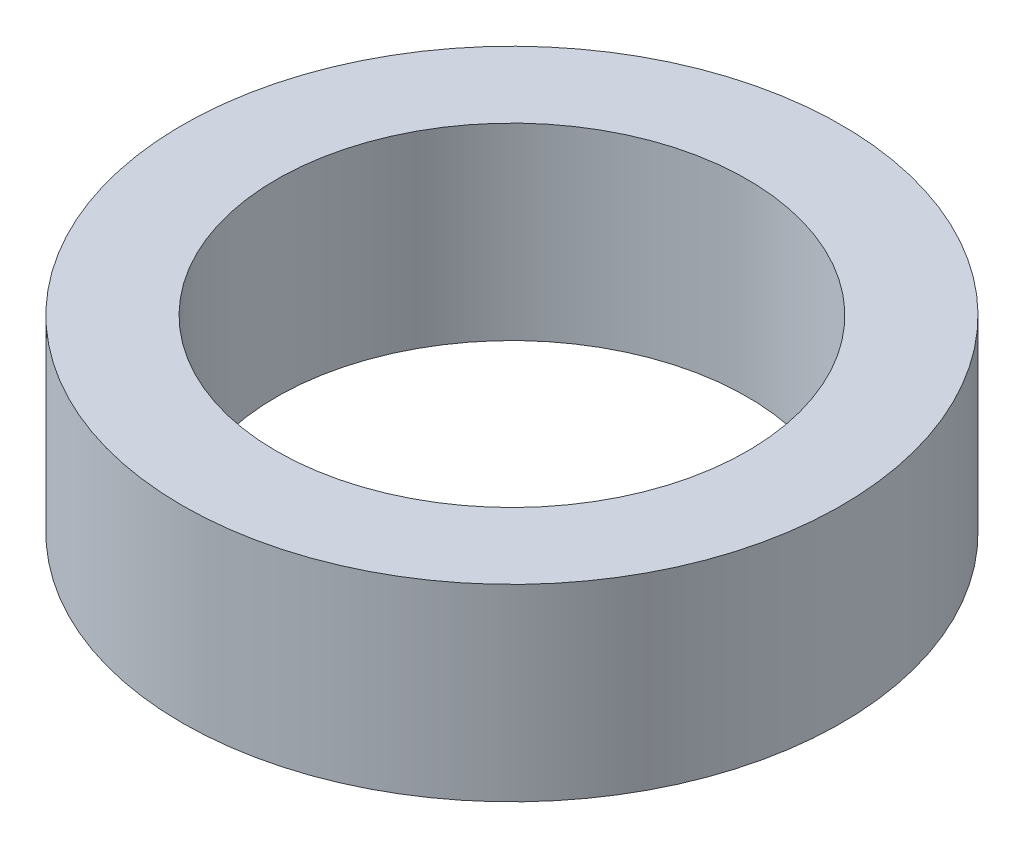
SolidWorks part; units mm, degrees
ref_plane "Front Plane" through (0, 0, 0) normal (0, 0, 1) x (1, 0, 0)
ref_plane "Top Plane" through (0, 0, 0) normal (0, 1, 0) x (1, 0, 0)
ref_plane "Right Plane" through (0, 0, 0) normal (1, 0, 0) x (0, 0, -1)
sketch "Sketch1" plane through (0, 0, 0) normal (0, 1, 0) x (1, 0, 0)
  line L0 (0, 15.875) -> (0, 22.225) construction
  circle A0 centre (0, 0) radius 15.875
  circle A1 centre (0, 0) radius 22.225
extrude "Boss-Extrude1" add sketch "Sketch1" along normal blind 12.7
